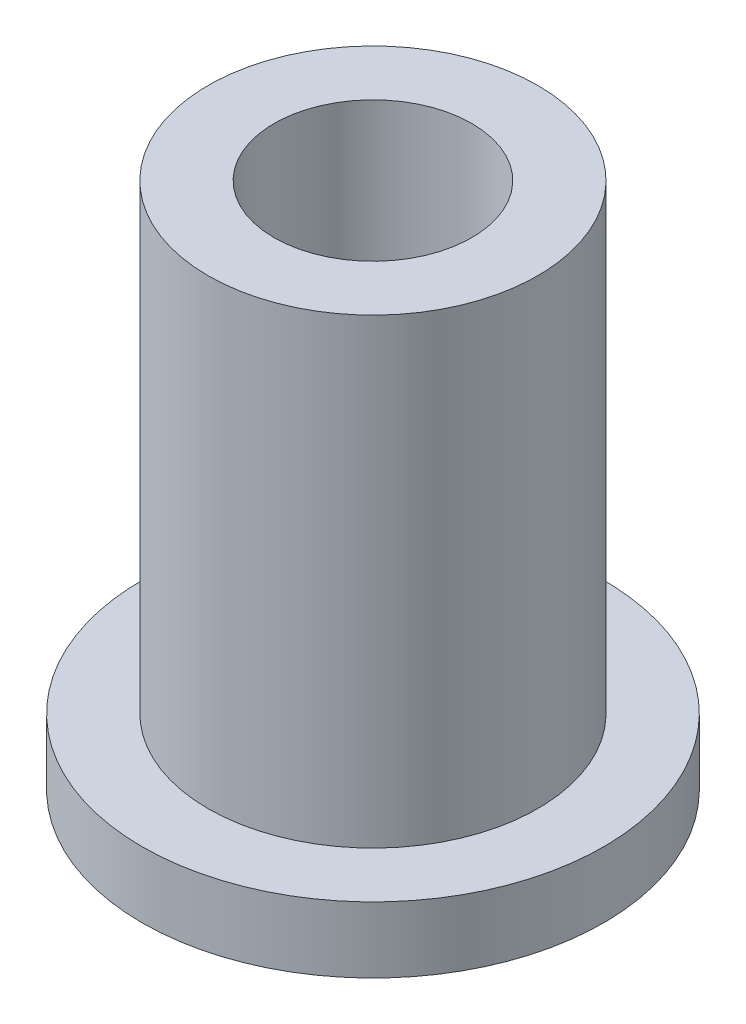
SolidWorks part; units mm, degrees
ref_plane "Front" through (0, 0, 0) normal (0, 0, 1) x (1, 0, 0)
ref_plane "Top" through (0, 0, 0) normal (0, 1, 0) x (1, 0, 0)
ref_plane "Right" through (0, 0, 0) normal (1, 0, 0) x (0, 0, -1)
sketch "Sketch1" plane through (0, 0, 0) normal (0, 1, 0) x (1, 0, 0)
  circle A0 centre (0, 0) radius 2.3813
  circle A1 centre (0, 0) radius 3.9688
  circle A2 centre (0, 0) radius 5.5562
  dimension "ID" = 4.7625
  dimension "OD" = 7.9375
  dimension "FlangeOD" = 11.1125
sketch "Sketch2" plane through (0, 0, 0) normal (0, 1, 0) x (1, 0, 0)
  circle A0 centre (0, 0) radius 2.3813 construction
  circle A1 centre (0, 0) radius 3.9688 construction
  circle A2 centre (0, 0) radius 2.3813
  circle A3 centre (0, 0) radius 3.9688
extrude "Boss-Extrude1" add sketch "Sketch2" along normal blind 12.7
sketch "Sketch3" plane through (0, 0, 0) normal (0, 1, 0) x (1, 0, 0)
  circle A0 centre (0, 0) radius 5.5562 construction
  circle A1 centre (0, 0) radius 3.9688 construction
  circle A2 centre (0, 0) radius 5.5562
  circle A3 centre (0, 0) radius 3.9688
extrude "Boss-Extrude2" add sketch "Sketch3" along normal blind 1.5875
